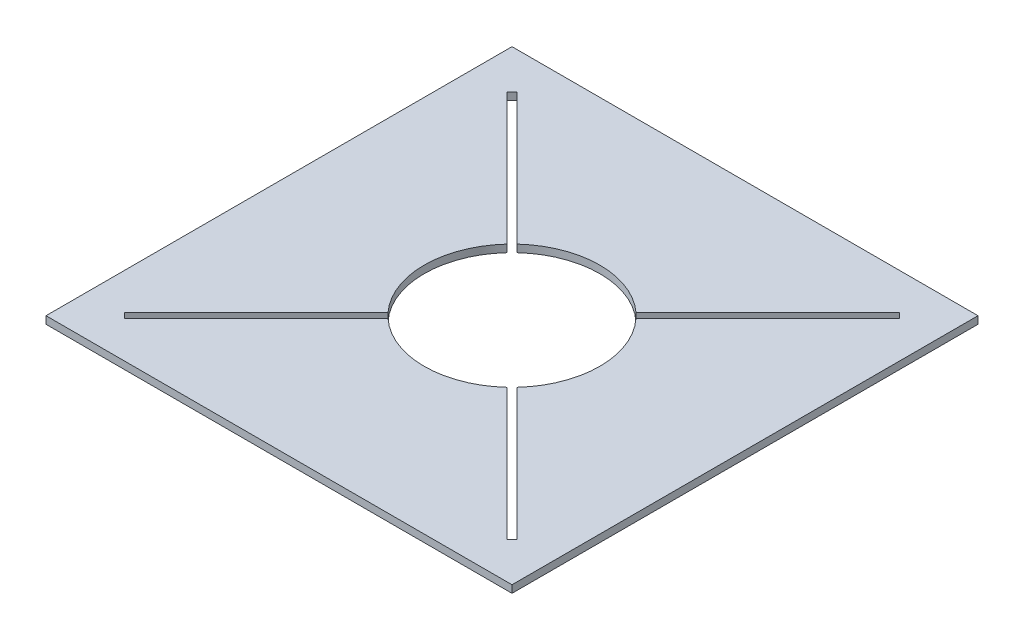
SolidWorks part; units mm, degrees
ref_plane "Front Plane" through (0, 0, 0) normal (0, 0, 1) x (1, 0, 0)
ref_plane "Top Plane" through (0, 0, 0) normal (0, 1, 0) x (1, 0, 0)
ref_plane "Right Plane" through (0, 0, 0) normal (1, 0, 0) x (0, 0, -1)
sketch "Sketch4" plane through (0, 0, 0) normal (0, 1, 0) x (1, 0, 0)
  line L1 (-206.5459, -206.5459) -> (206.5459, -206.5459)
  line L2 (-206.5459, -206.5459) -> (-206.5459, 206.5459)
  line L3 (-206.5459, 206.5459) -> (206.5459, 206.5459)
  line L4 (206.5459, -206.5459) -> (206.5459, 206.5459)
  line L5 (-206.5459, -206.5459) -> (206.5459, 206.5459) construction
  line L6 (-206.5459, 206.5459) -> (206.5459, -206.5459) construction
  circle A0 centre (0, 0) radius 77.7926
  point P0 (0, 0)
extrude "Boss-Extrude3" add sketch "Sketch4" along normal blind 6.604 contours L3 L4 L1 L2
sketch "Sketch6" plane through (0, 6.604, 0) normal (0, 1, 0) x (1, 0, 0)
  circle A0 centre (0, 0) radius 77.7926
extrude "Cut-Extrude1" cut sketch "Sketch6" against normal blind 6.604
sketch "Sketch8" plane through (0, 6.604, 0) normal (0, 1, 0) x (1, 0, 0)
  line L4 (-174.0553, -169.4574) -> (169.4574, 174.0553)
  line L5 (-174.0553, -169.4574) -> (-169.4574, -174.0553)
  line L6 (169.4574, 174.0553) -> (174.0553, 169.4574)
  line L7 (-169.4574, -174.0553) -> (174.0553, 169.4574)
  line L8 (-174.0553, -169.4574) -> (174.0553, 169.4574) construction
  line L9 (169.4574, 174.0553) -> (-169.4574, -174.0553) construction
  point P3 (0, 0)
extrude "Cut-Extrude2" cut sketch "Sketch8" against normal blind 6.604
sketch "Sketch9" plane through (0, 6.604, 0) normal (0, 1, 0) x (1, 0, 0)
  line L0 (174.0643, -169.4485) -> (-169.4485, 174.0643)
  line L1 (174.0643, -169.4485) -> (169.4485, -174.0643)
  line L2 (-169.4485, 174.0643) -> (-174.0643, 169.4485)
  line L3 (169.4485, -174.0643) -> (-174.0643, 169.4485)
  line L4 (174.0643, -169.4485) -> (-174.0643, 169.4485) construction
  line L5 (-169.4485, 174.0643) -> (169.4485, -174.0643) construction
  point P1 (0, 0)
extrude "Cut-Extrude3" cut sketch "Sketch9" against normal blind 6.604
